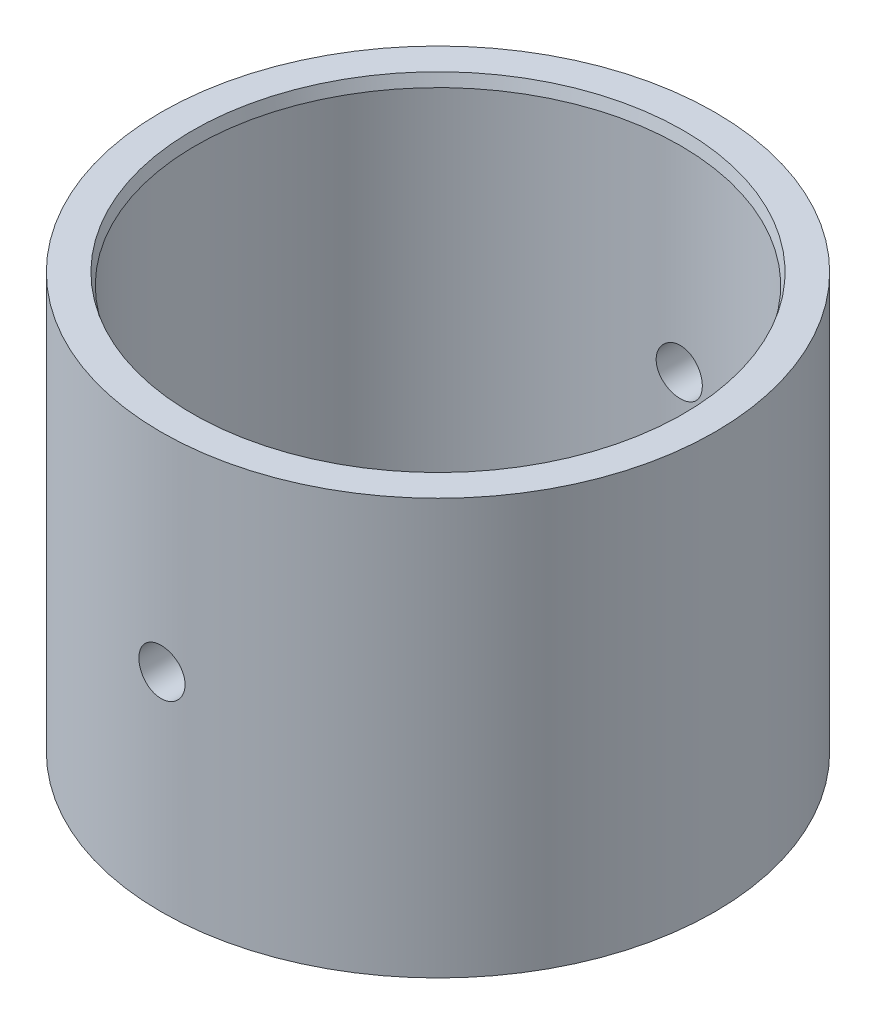
SolidWorks part; units mm, degrees
ref_plane "Plan de face" through (0, 0, 0) normal (0, 0, 1) x (1, 0, 0)
ref_plane "Plan de dessus" through (0, 0, 0) normal (0, 1, 0) x (1, 0, 0)
ref_plane "Plan de droite" through (0, 0, 0) normal (1, 0, 0) x (0, 0, -1)
sketch "Esquisse1" plane through (0, 0, 0) normal (0, 0, 1) x (1, 0, 0)
  line L0 (0, 0) -> (0, 36) construction
  line L1 (-24, 36) -> (-21.2679, 36)
  line L2 (-21, 35) -> (-21, 1)
  line L3 (-21.2679, 0) -> (-24, 0)
  line L4 (-24, 0) -> (-24, 36)
  line L5 (-21.2679, 36) -> (-21, 35)
  line L6 (-21, 1) -> (-21.2679, 0)
  point P4 (-21, 36)
  point P6 (-21, 0)
  dimension "D1" = 48
  dimension "D2" = 42
  dimension "D3" = 36
  dimension "D4" = 1
  dimension "D5" = 15
  dimension "D6" = 1
  dimension "D7" = 15
revolve "Révolution1" add sketch "Esquisse1" angle 360 about L0
sketch "Esquisse2" plane through (0, 0, 0) normal (0, 0, 1) x (1, 0, 0)
  circle A0 centre (0, 18) radius 2
  dimension "D1" = 18
  dimension "D2" = 4
  dimension "D3" = 0
extrude "Enlèv. mat.-Extru.1" cut sketch "Esquisse2" against normal through all both and the other way through all
